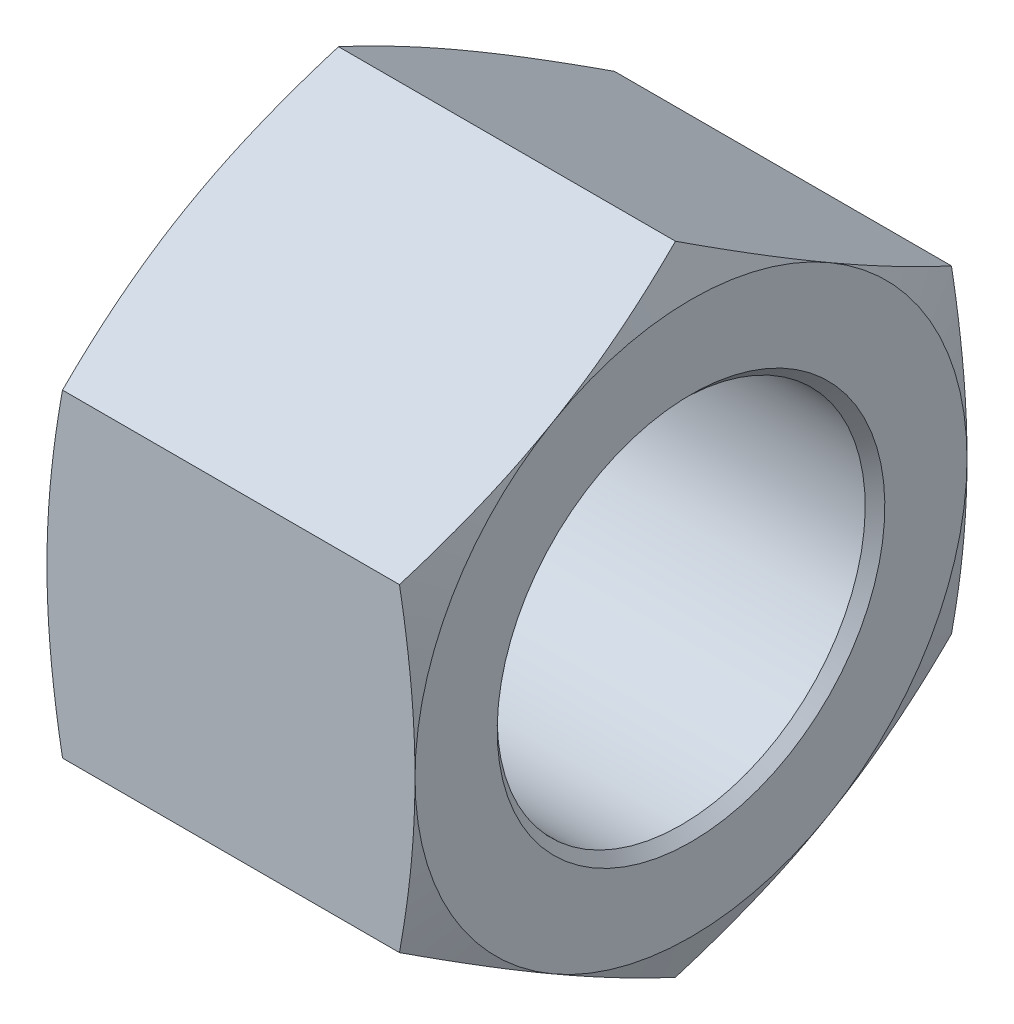
SolidWorks part; units mm, degrees
material "Cast Alloy Steel"
ref_plane "Front Plane" through (0, 0, 0) normal (0, 0, 1) x (1, 0, 0)
ref_plane "Top Plane" through (0, 0, 0) normal (0, 1, 0) x (1, 0, 0)
ref_plane "Right Plane" through (0, 0, 0) normal (1, 0, 0) x (0, 0, -1)
sketch "Sketch1" plane through (0, 0, 0) normal (1, 0, 0) x (0, 0, -1)
  line L1 (0, 8.2489) -> (-7.1438, 4.1244)
  line L2 (-7.1438, 4.1244) -> (-7.1438, -4.1244)
  line L3 (-7.1438, -4.1244) -> (0, -8.2489)
  line L4 (0, -8.2489) -> (7.1437, -4.1244)
  line L5 (7.1437, -4.1244) -> (7.1437, 4.1244)
  line L6 (7.1437, 4.1244) -> (0, 8.2489)
  circle A0 centre (0, 0) radius 7.1438 construction
  circle A1 centre (0, 0) radius 4.7625
  point P10 (-5.5191, 8.9982)
  dimension "D1" = 9.525
  dimension "D2" = 14.2875
extrude "Boss-Extrude1" add sketch "Sketch1" along normal blind 9.525
sketch "Sketch2" plane through (0, 0, 0) normal (0, 0, 1) x (1, 0, 0)
  line L0 (0, 7.1437) -> (0.4022, 8.2489)
  line L1 (0, 8.2489) -> (0, 4.1244) construction
  line L2 (9.525, 8.2489) -> (0, 8.2489) construction
  line L3 (0.4022, 8.2489) -> (0, 8.2489)
  line L4 (0, 8.2489) -> (0, 7.1437)
  line L5 (0, 4.7625) -> (0.254, 4.7625)
  line L6 (0, 4.1244) -> (0, -4.1244) construction
  line L7 (0.254, 4.7625) -> (0, 5.0165)
  line L8 (0, 5.0165) -> (0, 4.7625)
  line L9 (0, 0) -> (9.525, 0) construction
  line L10 (9.525, 4.1244) -> (9.525, -4.1244) construction
  line L11 (4.7625, 8.2489) -> (4.7625, -8.2489) construction
  line L12 (9.525, -8.2489) -> (0, -8.2489) construction
  line L15 (9.525, 5.0165) -> (9.525, 4.7625)
  line L16 (9.271, 4.7625) -> (9.525, 5.0165)
  line L17 (9.525, 4.7625) -> (9.271, 4.7625)
  line L18 (9.525, 8.2489) -> (9.525, 7.1438)
  line L19 (9.1228, 8.2489) -> (9.525, 8.2489)
  line L20 (9.525, 7.1438) -> (9.1228, 8.2489)
  point P22 (0, 4.2044)
  point P25 (0, 0)
  dimension "D1" = 0.254
  dimension "D2" = 20
  dimension "D3" = 14.2875
revolve "Cut-Revolve1" cut sketch "Sketch2" angle 360 about L9
